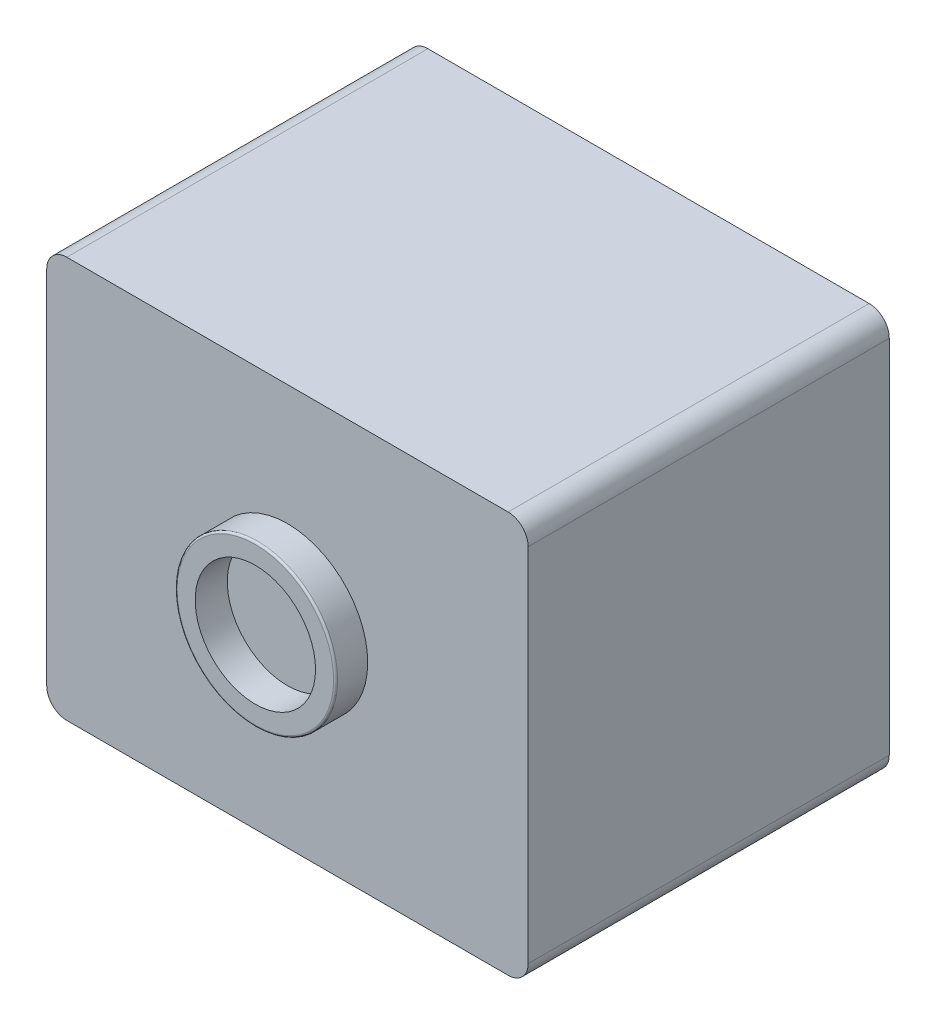
SolidWorks part; units mm, degrees
other "标注1"
sketch "草图8" plane through (6, -5, 9.8) normal (0.0379, -0.1881, 0.9814) x (0.988, -0.1402, -0.065)
ref_plane "前视基准面" through (0, 0, 0) normal (0, 0, 1) x (1, 0, 0)
ref_plane "上视基准面" through (0, 0, 0) normal (0, 1, 0) x (1, 0, 0)
ref_plane "右视基准面" through (0, 0, 0) normal (1, 0, 0) x (0, 0, -1)
sketch "草图1" plane through (0, 0, 0) normal (0, 0, 1) x (1, 0, 0)
  line L1 (-6, -5) -> (6, -5)
  line L2 (-6, -5) -> (-6, 5)
  line L3 (-6, 5) -> (6, 5)
  line L4 (6, -5) -> (6, 5)
  line L5 (-6, -5) -> (6, 5) construction
  line L6 (-6, 5) -> (6, -5) construction
  point P0 (0, 0)
  dimension "D1" = 12
  dimension "D2" = 10
extrude "凸台-拉伸1" add sketch "草图1" along normal blind 9
fillet "圆角1" radius 0.5 4 edges at (6, -5, 4.5) (-6, -5, 4.5) (-6, 5, 4.5) (6, 5, 4.5)
sketch "草图2" plane through (0, 0, 9) normal (0, 0, 1) x (1, 0, 0)
  circle A0 centre (0, 0) radius 1.5
  circle A1 centre (0, 0) radius 2
extrude "凸台-拉伸2" add sketch "草图2" along normal blind 0.8
fillet "圆角2" radius 0.05 1 edges at (2, 0, 9.8)
sketch "草图3" plane through (0, 0, 9) normal (0, 0, 1) x (1, 0, 0)
  circle A0 centre (0, 0) radius 1.5
sketch "草图7" plane through (0, 0, 0) normal (0, 0, -1) x (-1, 0, 0)
  circle A0 centre (0, 0) radius 2
extrude "切除-拉伸4" cut sketch "草图7" against normal blind 0.1
